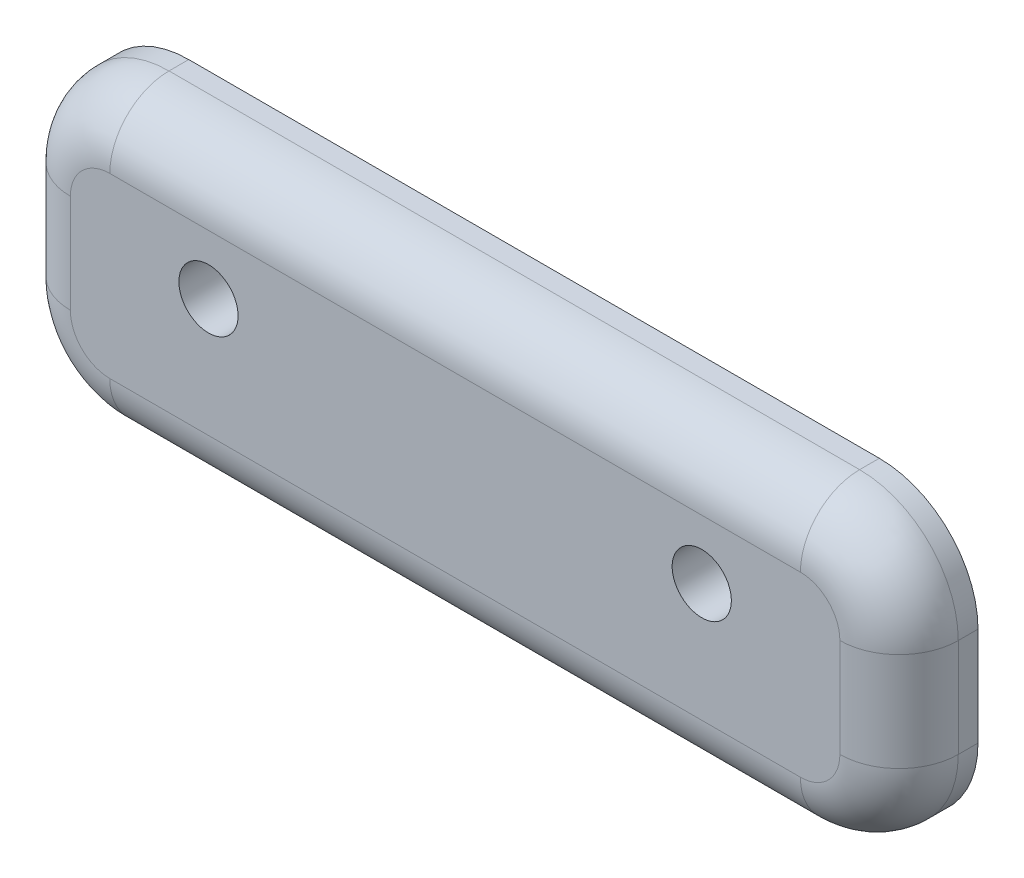
SolidWorks part; units mm, degrees
material "Alliage 2018"
ref_plane "Plan de face" through (0, 0, 0) normal (0, 0, 1) x (1, 0, 0)
ref_plane "Plan de dessus" through (0, 0, 0) normal (0, 1, 0) x (1, 0, 0)
ref_plane "Plan de droite" through (0, 0, 0) normal (1, 0, 0) x (0, 0, -1)
sketch "Esquisse1" plane through (0, 0, 0) normal (0, 0, 1) x (1, 0, 0)
  line L1 (22.5, -7.5) -> (-22.5, -7.5)
  line L2 (22.5, -7.5) -> (22.5, 7.5)
  line L3 (22.5, 7.5) -> (-22.5, 7.5)
  line L4 (-22.5, -7.5) -> (-22.5, 7.5)
  line L5 (22.5, -7.5) -> (-22.5, 7.5) construction
  line L6 (22.5, 7.5) -> (-22.5, -7.5) construction
  point P0 (0, 0)
  dimension "D1" = 45
  dimension "D2" = 15
extrude "Boss.-Extru.1" add sketch "Esquisse1" along normal blind 4
sketch "Esquisse2" plane through (0, 0, 4) normal (0, 0, 1) x (1, 0, 0)
  line L0 (22.5, 1.5) -> (-22.5, 1.5) construction
  line L1 (22.5, -7.5) -> (22.5, 7.5) construction
  line L2 (-22.5, 7.5) -> (-22.5, -7.5) construction
  line L3 (-12.5, 7.5) -> (-12.5, -7.5) construction
  line L4 (22.5, 7.5) -> (-22.5, 7.5) construction
  line L5 (-22.5, -7.5) -> (22.5, -7.5) construction
  line L6 (12.5, 7.5) -> (12.5, -7.5) construction
  circle A0 centre (-12.5, 1.5) radius 1.5
  circle A1 centre (12.5, 1.5) radius 1.5
  dimension "D4" = 3
  dimension "D5" = 3
  dimension "D1" = 10
  dimension "D2" = 10
  dimension "D3" = 6
fillet "Congé1" radius 5 4 edges at (22.5, -7.5, 2) (-22.5, -7.5, 2) (-22.5, 7.5, 2) (22.5, 7.5, 2)
fillet "Congé2" radius 3 8 edges at (-21.0355, -6.0355, 4) (-22.5, 0, 4) (-21.0355, 6.0355, 4) (0, 7.5, 4) (21.0355, 6.0355, 4) (22.5, 0, 4) (21.0355, -6.0355, 4) (0, -7.5, 4)
extrude "Enlèv. mat.-Extru.1" cut sketch "Esquisse2" against normal through all
